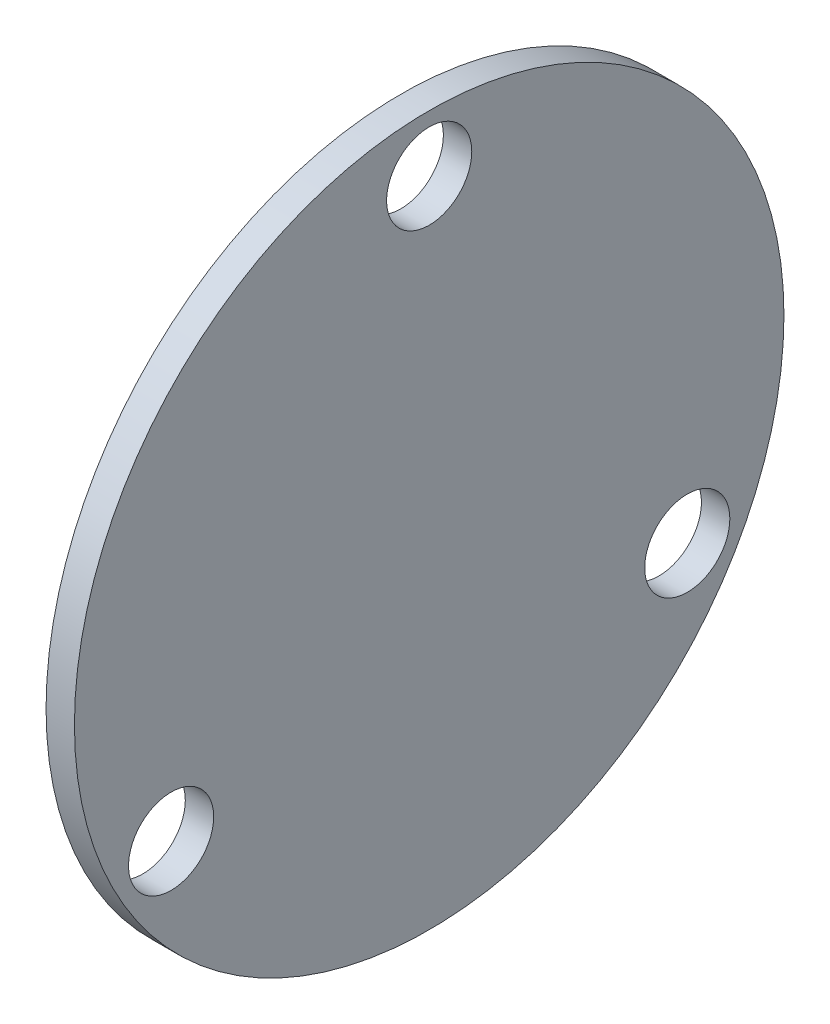
SolidWorks part; units mm, degrees
material "1.0301 (C10)"
ref_plane "Plan de face" through (0, 0, 0) normal (0, 0, 1) x (1, 0, 0)
ref_plane "Plan de dessus" through (0, 0, 0) normal (0, 1, 0) x (1, 0, 0)
ref_plane "Plan de droite" through (0, 0, 0) normal (1, 0, 0) x (0, 0, -1)
sketch "Esquisse1" plane through (0, 0, 0) normal (1, 0, 0) x (0, 0, -1)
  circle A0 centre (0, 0) radius 12.5
  dimension "D1" = 25
extrude "Boss.-Extru.1" add sketch "Esquisse1" along normal blind 1
sketch "Esquisse2" plane through (1, 0, 0) normal (1, 0, 0) x (0, 0, -1)
  circle A0 centre (0, 10.5) radius 1.5
  circle A1 centre (9.0933, -5.25) radius 1.5
  circle A2 centre (-9.0933, -5.25) radius 1.5
  point P9 (0, 0)
  dimension "D3" = 3
  dimension "D1" = 0
  dimension "D2" = 10.5
  dimension "D4" = 3
extrude "Enlèv. mat.-Extru.1" cut sketch "Esquisse2" against normal blind 1
